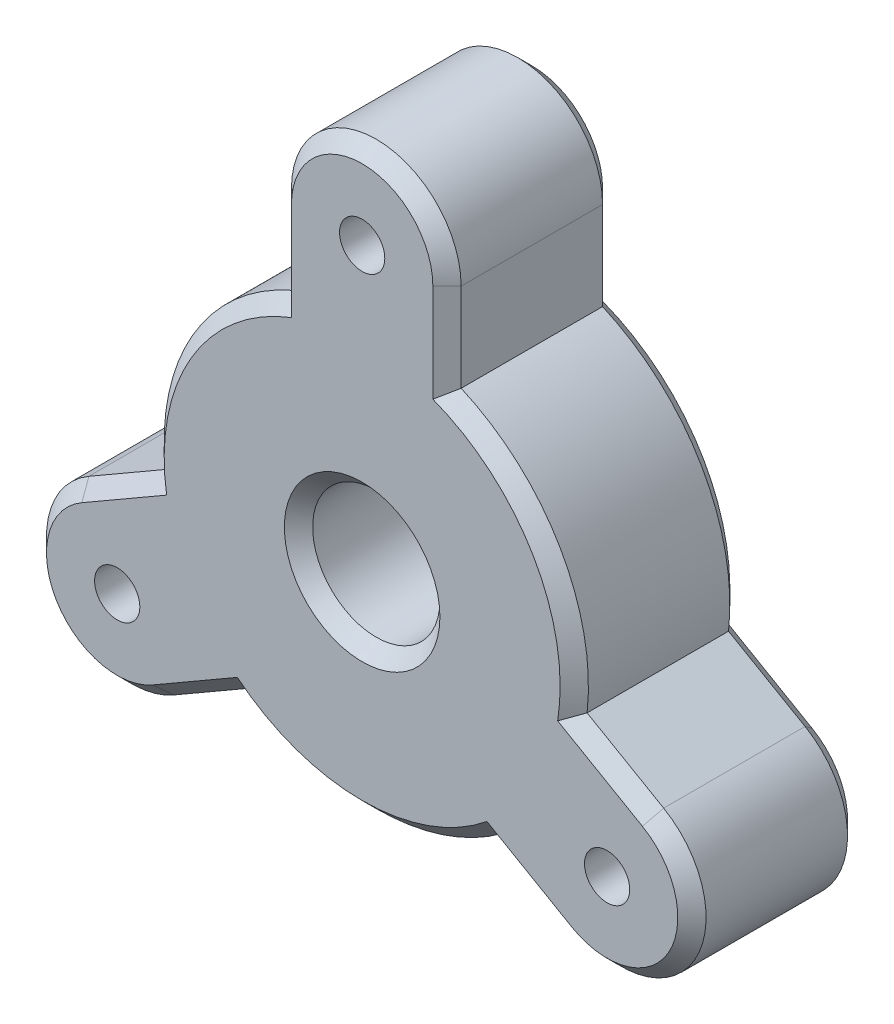
SolidWorks part; units mm, degrees
material "ABS"
ref_plane "Front Plane" through (0, 0, 0) normal (0, 0, 1) x (1, 0, 0)
ref_plane "Top Plane" through (0, 0, 0) normal (0, 1, 0) x (1, 0, 0)
ref_plane "Right Plane" through (0, 0, 0) normal (1, 0, 0) x (0, 0, -1)
sketch "Sketch1" plane through (0, 0, 0) normal (0, 0, 1) x (1, 0, 0)
  circle A0 centre (0, 0) radius 15
  dimension "D1" = 30
sketch "Sketch2" plane through (0, 0, 0) normal (0, 0, 1) x (1, 0, 0)
  line L0 (0, 0) -> (0, 20) construction
  line L1 (-6, 20) -> (6, 20) construction
  line L2 (-6, 20) -> (-6, 13.7477)
  line L3 (6, 20) -> (6, 13.7477)
  line L4 (-6, 13.7477) -> (6, 13.7477)
  line L5 (20.3205, -4.8038) -> (14.9059, -1.6777)
  line L6 (14.3205, -15.1962) -> (8.9059, -12.07)
  line L7 (14.9059, -1.6777) -> (8.9059, -12.07)
  line L8 (20.3205, -4.8038) -> (14.3205, -15.1962) construction
  line L9 (-14.3205, -15.1962) -> (-8.9059, -12.07)
  line L10 (-20.3205, -4.8038) -> (-14.9059, -1.6777)
  line L11 (-8.9059, -12.07) -> (-14.9059, -1.6777)
  line L12 (-14.3205, -15.1962) -> (-20.3205, -4.8038) construction
  circle A0 centre (0, 0) radius 15 construction
  arc A2 (6, 20) -> (-6, 20) centre (0, 20) ccw
  arc A3 (14.3205, -15.1962) -> (20.3205, -4.8038) centre (17.3205, -10) ccw
  arc A4 (-20.3205, -4.8038) -> (-14.3205, -15.1962) centre (-17.3205, -10) ccw
  point P5 (0, 20)
  point P22 (0, 0)
  dimension "D1" = 12
  dimension "D2" = 20
  dimension "D3" = 3
sketch "Sketch3" plane through (0, 0, 0) normal (0, 0, 1) x (1, 0, 0)
  circle A0 centre (0, 0) radius 4.5
  dimension "D1" = 9
extrude "Boss-Extrude1" add sketch "Sketch1" along normal mid plane 12
extrude "Boss-Extrude2" add sketch "Sketch2" along normal up to surface and the other way up to surface up to face at (15, 0, 6) other way up to face at (15, 0, -6)
extrude "Cut-Extrude1" cut sketch "Sketch3" along normal through all and the other way through all
chamfer "Chamfer1" distance 1 angle 45 26 edges at (4.5, 0, 6) (4.5, 0, -6) (-6, 16.8739, 6) (-6, 16.8739, -6) (0, 26, 6) (0, 26, -6) (6, 16.8739, 6) (6, 16.8739, -6) (12.9904, 7.5, -6) (12.9904, 7.5, 6) (17.6132, -3.2408, 6) (17.6132, -3.2408, -6) (22.5167, -13, 6) (22.5167, -13, -6) (11.6132, -13.6331, 6) (11.6132, -13.6331, -6) (0, -15, -6) (0, -15, 6) (-11.6132, -13.6331, 6) (-11.6132, -13.6331, -6) (-22.5167, -13, 6) (-22.5167, -13, -6) (-17.6132, -3.2408, 6) (-17.6132, -3.2408, -6) (-12.9904, 7.5, -6) (-12.9904, 7.5, 6)
sketch "Sketch4" plane through (0, 0, 0) normal (0, 0, 1) x (1, 0, 0)
  circle A0 centre (0, 20) radius 1.6
  circle A1 centre (17.3205, -10) radius 1.6
  circle A2 centre (-17.3205, -10) radius 1.6
  arc A3 (-14.3205, -15.1962) -> (-20.3205, -4.8038) centre (-17.3205, -10) ccw construction
  arc A4 (-6, 20) -> (6, 20) centre (0, 20) ccw construction
  arc A5 (20.3205, -4.8038) -> (14.3205, -15.1962) centre (17.3205, -10) ccw construction
  dimension "D1" = 3.2
extrude "Cut-Extrude2" cut sketch "Sketch4" along normal through all and the other way through all
